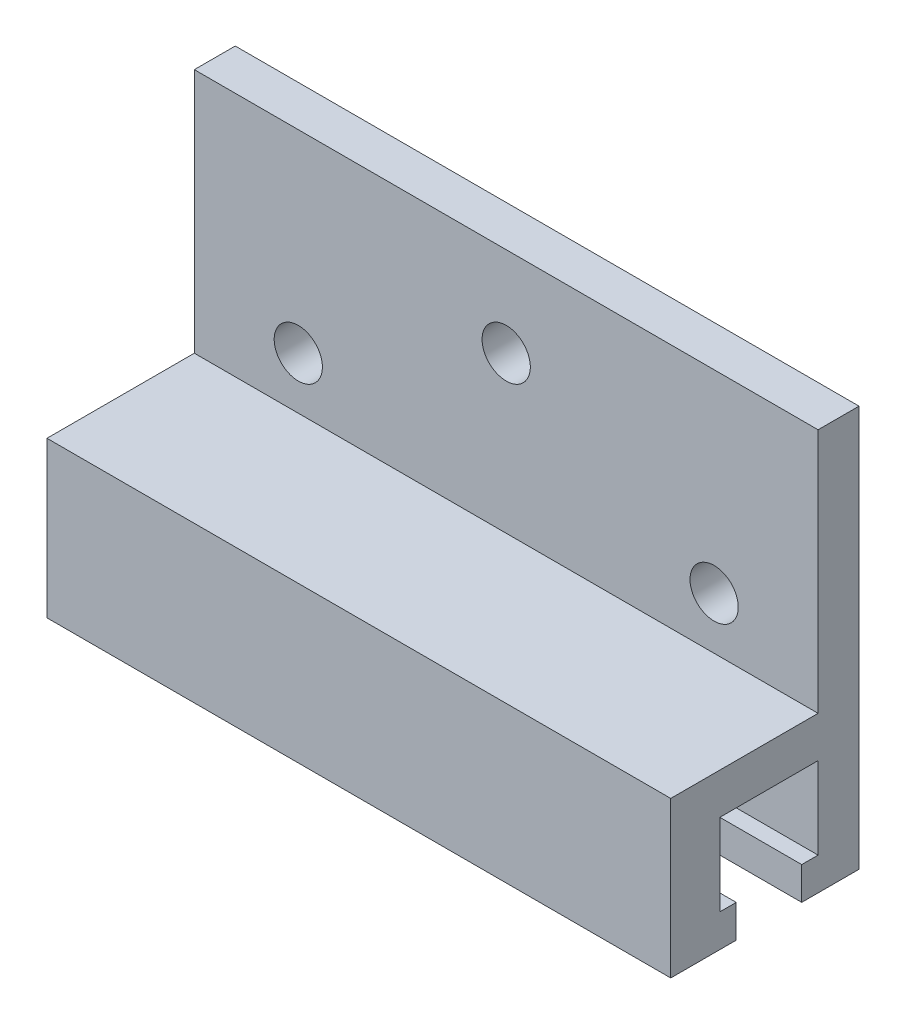
SolidWorks part; units mm, degrees
ref_plane "Front Plane" through (0, 0, 0) normal (0, 0, 1) x (1, 0, 0)
ref_plane "Top Plane" through (0, 0, 0) normal (0, 1, 0) x (1, 0, 0)
ref_plane "Right Plane" through (0, 0, 0) normal (1, 0, 0) x (0, 0, -1)
sketch "Sketch1" plane through (0, 0, 0) normal (1, 0, 0) x (0, 0, -1)
  line L0 (-6, -4.5) -> (-2, -4.5)
  line L1 (-3, 2.5) -> (3, 2.5)
  line L2 (-3, 2.5) -> (-3, -2.5)
  line L3 (-3, -2.5) -> (-2, -2.5)
  line L4 (3, 2.5) -> (3, -2.5)
  line L5 (-3, 2.5) -> (3, -2.5) construction
  line L6 (-3, -2.5) -> (3, 2.5) construction
  line L7 (-6, 5) -> (3, 5)
  line L8 (-6, 5) -> (-6, -4.5)
  line L9 (2, -2.5) -> (3, -2.5)
  line L10 (5.5, 4.5833) -> (5.5, -4.5)
  line L11 (-6, 5) -> (5.5, -4.5833) construction
  line L12 (-6, -5) -> (5.5, 4.5833) construction
  line L13 (-2, -2.5) -> (-2, -4.5)
  line L14 (2, -2.5) -> (2, -4.5)
  line L15 (-2, -3.5) -> (2, -3.5) construction
  line L16 (2, -4.5) -> (5.5, -4.5)
  line L17 (3, 5) -> (3, 20)
  line L18 (3, 20) -> (5.5, 20)
  line L19 (5.5, 20) -> (5.5, 4.5833)
  point P0 (0, 0)
  point P6 (0, 0)
  point P19 (0, -3.5)
  dimension "D1" = 6
  dimension "D2" = 9.5
  dimension "D3" = 2.5
  dimension "D4" = 2.5
  dimension "D5" = 2
  dimension "D6" = 4
  dimension "D7" = 24.5
extrude "Boss-Extrude1" add sketch "Sketch1" along normal blind 38.1
hole_wizard "#4 Clearance Hole1" positions "Sketch4" profile "Sketch3" hole size "#4" standard "ANSI Inch"
sketch "Sketch4" plane through (0, 0, -5.5) normal (0, 0, -1) x (-1, 0, 0)
  line L0 (-38.1, 20) -> (0, 20) construction
  line L1 (-31.75, 8.175) -> (-6.35, 8.175) construction
  line L2 (-38.1, 5) -> (0, 5) construction
  point P0 (-19.05, 14.525)
  point P2 (-31.75, 8.175)
  point P4 (-6.35, 8.175)
  point P9 (-19.05, 20)
  point P15 (-19.05, 8.175)
  dimension "D1" = 25.4
  dimension "D2" = 6.35
  dimension "D3" = 9.525
sketch "Sketch3" plane through (19.05, 14.525, -5.5) normal (1, 0, 0) x (0, 1, 0)
  line L0 (0, 0) -> (0, 7.2352)
  line L1 (0, 7.2352) -> (1.4732, 6.35)
  line L2 (1.4732, 6.35) -> (1.4732, 0)
  line L5 (1.4732, 0) -> (0, 0)
  line L10 (0, 7.2352) -> (-1.4732, 6.35) construction
  line L11 (0, -6.35) -> (0, 107.95) construction
  dimension "Hole Dia." = 2.9464
  dimension "Hole Depth" = 6.35
  dimension "Drill Angle" = 118
